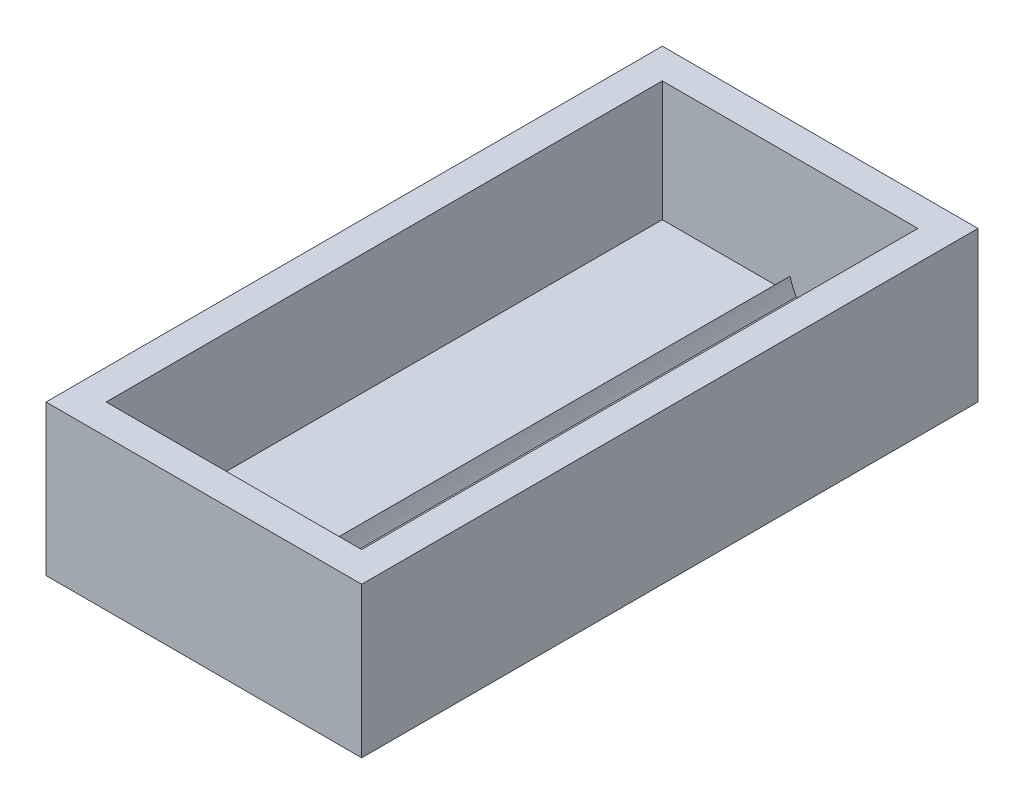
SolidWorks part; units mm, degrees
ref_plane "Front Plane" through (0, 0, 0) normal (0, 0, 1) x (1, 0, 0)
ref_plane "Top Plane" through (0, 0, 0) normal (0, 1, 0) x (1, 0, 0)
ref_plane "Right Plane" through (0, 0, 0) normal (1, 0, 0) x (0, 0, -1)
sketch "Sketch1" plane through (0, 0, 0) normal (0, 1, 0) x (1, 0, 0)
  line L1 (0, 0) -> (26.67, 0)
  line L2 (0, 0) -> (0, 52.07)
  line L3 (0, 52.07) -> (26.67, 52.07)
  line L4 (26.67, 0) -> (26.67, 52.07)
  dimension "D1" = 26.67
  dimension "D2" = 52.07
extrude "Boss-Extrude1" add sketch "Sketch1" along normal blind 12.7
sketch "Sketch2" plane through (0, 12.7, 0) normal (0, 1, 0) x (1, 0, 0)
  line L0 (0, 52.07) -> (0, 0) construction
  line L1 (2.54, 2.54) -> (24.13, 2.54)
  line L2 (2.54, 2.54) -> (2.54, 49.53)
  line L3 (2.54, 49.53) -> (24.13, 49.53)
  line L4 (24.13, 2.54) -> (24.13, 49.53)
  line L5 (26.67, 52.07) -> (0, 52.07) construction
  dimension "D1" = 21.59
  dimension "D2" = 46.99
  dimension "D3" = 2.54
  dimension "D4" = 2.54
extrude "Cut-Extrude1" cut sketch "Sketch2" against normal blind 10.16
sketch "Sketch4" plane through (0, 0, 0) normal (0, 0, 1) x (1, 0, 0)
  line L0 (13.335, 0) -> (13.335, 3.81) construction
  line L1 (0, 0) -> (26.67, 0) construction
  line L2 (8.89, 0) -> (17.78, 0)
  arc A0 (17.78, 0) -> (13.335, 3.81) centre (18.2595, 5.0573) cw
  arc A1 (8.89, 0) -> (13.335, 3.81) centre (8.4105, 5.0573) ccw
  point P5 (0, 0)
  point P7 (13.3372, 5.08)
  point P10 (0, 0)
  point P11 (8.9748, 0)
  point P12 (0, 0)
  point P13 (13.335, 3.81)
  dimension "D1" = 3.81
  dimension "D2" = 8.89
  dimension "D3" = 4.445
extrude "Boss-Extrude2" add sketch "Sketch4" against normal through all
